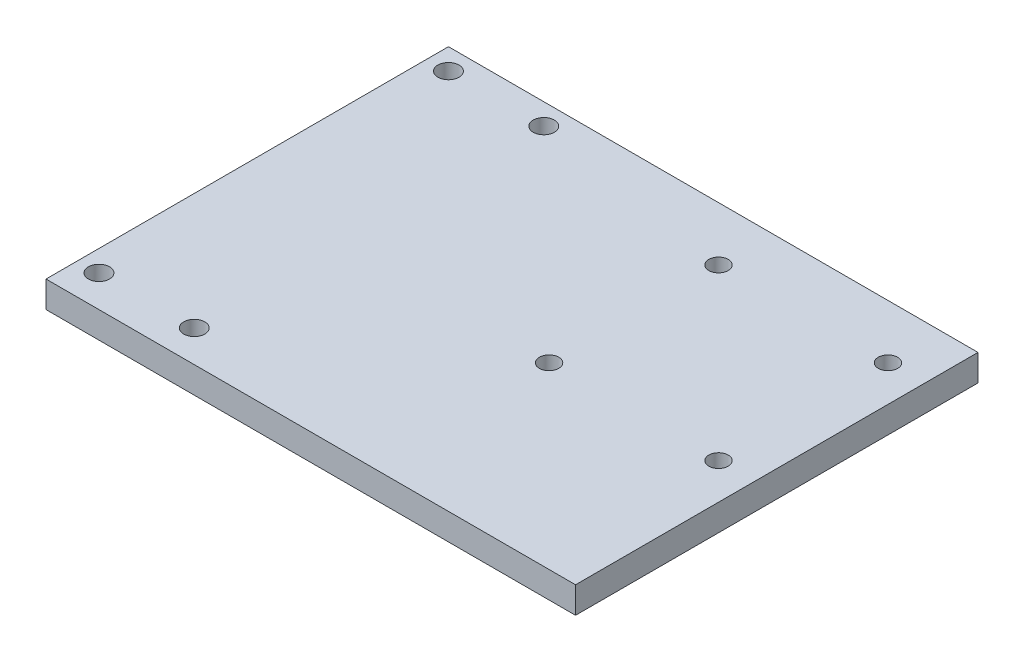
SolidWorks part; units mm, degrees
ref_plane "Front" through (0, 0, 0) normal (0, 0, 1) x (1, 0, 0)
ref_plane "Top" through (0, 0, 0) normal (0, 1, 0) x (1, 0, 0)
ref_plane "Right" through (0, 0, 0) normal (1, 0, 0) x (0, 0, -1)
sketch "Sketch1" plane through (0, 0, 0) normal (0, 1, 0) x (1, 0, 0)
  line L1 (-50, -38) -> (50, -38)
  line L2 (-50, -38) -> (-50, 38)
  line L3 (-50, 38) -> (50, 38)
  line L4 (50, -38) -> (50, 38)
  line L5 (-50, -38) -> (50, 38) construction
  line L6 (-50, 38) -> (50, -38) construction
  point P0 (0, 0)
  dimension "D1" = 100
  dimension "D2" = 76
extrude "Boss-Extrude1" add sketch "Sketch1" along normal blind 5
sketch "Sketch2" plane through (0, 5, 0) normal (0, 1, 0) x (1, 0, 0)
  line L0 (50, 38) -> (-50, 38) construction
  line L1 (-50, 38) -> (-50, -38) construction
  circle A0 centre (-46, 34) radius 2
  circle A1 centre (-28, 34) radius 2
  circle A2 centre (-46, -32) radius 2
  circle A3 centre (-28, -32) radius 2
  circle A4 centre (11.2, 27.8) radius 1.8324
  circle A5 centre (43.2, 27.8) radius 1.8324
  circle A6 centre (11.2, -4.2) radius 1.8324
  circle A7 centre (43.2, -4.2) radius 1.8324
  dimension "D1" = 4
  dimension "D7" = 10.2
  dimension "D2" = 4
  dimension "D3" = 4
  dimension "D6" = 39.2
  dimension "D4" = 2
  dimension "D5" = 2
  dimension "D8" = 2
  dimension "D9" = 2
extrude "Cut-Extrude6" cut sketch "Sketch2" against normal up to next
